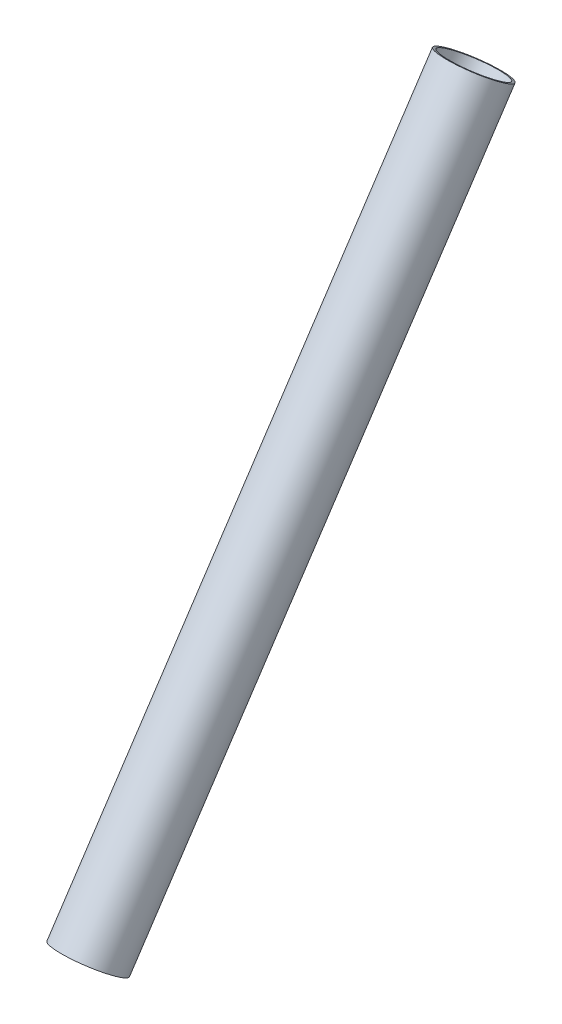
SolidWorks part; units mm, degrees
ref_plane "Front Plane" through (0, 0, 0) normal (0, 0, 1) x (1, 0, 0)
ref_plane "Top Plane" through (0, 0, 0) normal (0, 1, 0) x (1, 0, 0)
ref_plane "Right Plane" through (0, 0, 0) normal (1, 0, 0) x (0, 0, -1)
ref_plane "Plane1" through (0.3164, -246.1731, 163.8061) normal (0.0011, -0.8325, 0.554) x (-1, -0.0007, 0.0009)
sketch "Sketch2" plane through (0.3164, -246.1731, 163.8061) normal (0.0011, -0.8325, 0.554) x (-1, -0.0007, 0.0009)
  circle A0 centre (-29.4419, -1529.5929) radius 9.6012
  circle A1 centre (-29.4419, -1529.5929) radius 8.8138
extrude "Boss-Extrude1" add sketch "Sketch2" along normal up to vertex (210.3671 mm away)
